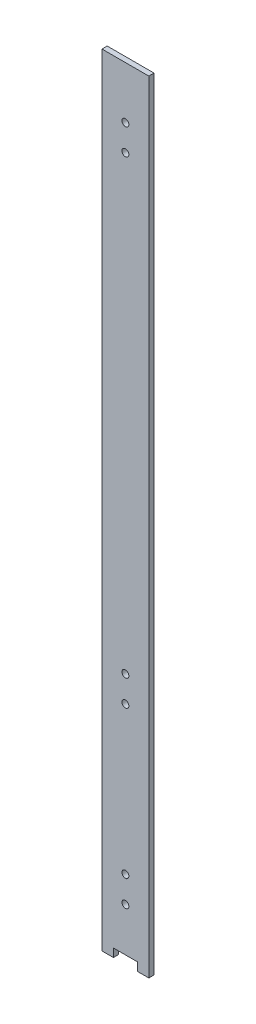
SolidWorks part; units mm, degrees
ref_plane "Front" through (0, 0, 0) normal (0, 0, 1) x (1, 0, 0)
ref_plane "Top" through (0, 0, 0) normal (0, 1, 0) x (1, 0, 0)
ref_plane "Right" through (0, 0, 0) normal (1, 0, 0) x (0, 0, -1)
sketch "草图1" plane through (0, 0, 0) normal (0, 1, 0) x (1, 0, 0)
  line L1 (13.5, -1.5) -> (-13.5, -1.5)
  line L2 (13.5, -1.5) -> (13.5, 1.5)
  line L3 (13.5, 1.5) -> (-13.5, 1.5)
  line L4 (-13.5, -1.5) -> (-13.5, 1.5)
  line L5 (13.5, -1.5) -> (-13.5, 1.5) construction
  line L6 (13.5, 1.5) -> (-13.5, -1.5) construction
  point P0 (0, 0)
  dimension "D1" = 3
  dimension "D2" = 27
extrude "凸台-拉伸1" add sketch "草图1" along normal blind 450
sketch "草图2" plane through (0, 0, -1.5) normal (0, 0, -1) x (-1, 0, 0)
  line L1 (6.9153, -4.7791) -> (-6.9153, -4.7791)
  line L2 (6.9153, -4.7791) -> (6.9153, 4.7791)
  line L3 (6.9153, 4.7791) -> (-6.9153, 4.7791)
  line L4 (-6.9153, -4.7791) -> (-6.9153, 4.7791)
  line L5 (6.9153, -4.7791) -> (-6.9153, 4.7791) construction
  line L6 (6.9153, 4.7791) -> (-6.9153, -4.7791) construction
  point P0 (0, 0)
extrude "切除-拉伸1" cut sketch "草图2" against normal through all
sketch "草图3" plane through (0, 0, -1.5) normal (0, 0, -1) x (-1, 0, 0)
  line L0 (0, 0) -> (0, 450) construction
  line L1 (-13.5, 450) -> (13.5, 450) construction
  line L2 (6.9153, 0) -> (13.5, 0) construction
  line L3 (-13.5, 0) -> (-6.9153, 0) construction
  circle A0 centre (0, 420) radius 2
  circle A1 centre (0, 405) radius 2
  circle A2 centre (0, 30) radius 2
  circle A3 centre (0, 45) radius 2
  circle A4 centre (0, 130) radius 2
  circle A5 centre (0, 145) radius 2
  dimension "D1" = 4
  dimension "D2" = 4
  dimension "D3" = 4
  dimension "D4" = 4
  dimension "D5" = 4
  dimension "D6" = 4
  dimension "D7" = 30
  dimension "D8" = 45
  dimension "D9" = 100
  dimension "D10" = 15
  dimension "D11" = 30
  dimension "D12" = 15
extrude "切除-拉伸2" cut sketch "草图3" against normal through all
